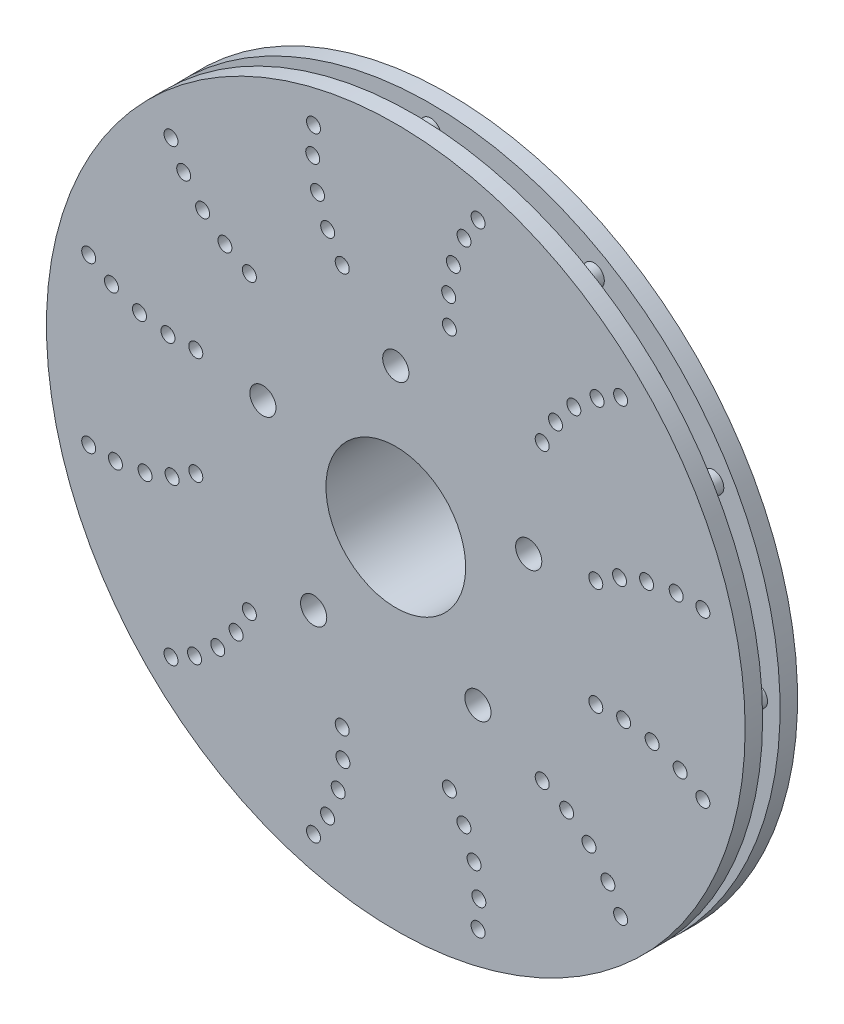
SolidWorks part; units mm, degrees
ref_plane "Front Plane" through (0, 0, 0) normal (0, 0, 1) x (1, 0, 0)
ref_plane "Top Plane" through (0, 0, 0) normal (0, 1, 0) x (1, 0, 0)
ref_plane "Right Plane" through (0, 0, 0) normal (1, 0, 0) x (0, 0, -1)
sketch "Sketch2" plane through (0, 0, 0) normal (0, 0, 1) x (1, 0, 0)
  circle A0 centre (-45.113, 24.0075) radius 25.4
  circle A1 centre (-45.113, 24.0075) radius 60.325
  circle A2 centre (3.2006, 39.7056) radius 4.7625
  circle A3 centre (-45.113, 74.8075) radius 4.7625
  circle A4 centre (-15.2535, -17.0905) radius 4.7625
  circle A5 centre (-74.9725, -17.0905) radius 4.7625
  circle A6 centre (-93.4267, 39.7056) radius 4.7625
extrude "Boss-Extrude1" add sketch "Sketch2" along normal blind 50.8
sketch "Sketch4" plane through (0, 0, 50.8) normal (0, 0, 1) x (1, 0, 0)
  circle A0 centre (-45.113, 24.0075) radius 127
  circle A1 centre (-45.113, 24.0075) radius 60.325
  dimension "D1" = 254
extrude "Boss-Extrude2" add sketch "Sketch4" against normal blind 6.35
sketch "Sketch5" plane through (0, 0, 44.45) normal (0, 0, -1) x (-1, 0, 0)
  line L0 (101.1439, 128.6428) -> (80.2798, 92.5051)
  line L1 (107.7144, 124.8493) -> (86.8503, 88.7117)
  line L2 (48.9065, 142.6398) -> (48.9065, 100.9116)
  line L3 (41.3196, 142.6398) -> (41.3196, 100.9116)
  line L4 (145.9549, 86.6089) -> (109.8172, 65.7448)
  line L5 (149.7483, 80.0384) -> (113.6106, 59.1743)
  line L6 (163.7453, 27.801) -> (122.0171, 27.801)
  line L7 (163.7453, 20.214) -> (122.0171, 20.214)
  line L8 (149.7483, -32.0234) -> (113.6106, -11.1593)
  line L9 (145.9549, -38.5939) -> (109.8172, -17.7298)
  line L10 (107.7144, -76.8343) -> (86.8503, -40.6966)
  line L11 (101.1439, -80.6278) -> (80.2798, -44.4901)
  line L12 (48.9065, -94.6248) -> (48.9065, -52.8965)
  line L13 (41.3196, -94.6248) -> (41.3196, -52.8965)
  line L14 (-10.9179, -80.6278) -> (9.9462, -44.4901)
  line L15 (-17.4884, -76.8343) -> (3.3758, -40.6966)
  line L16 (-55.7288, -38.5939) -> (-19.5911, -17.7298)
  line L17 (-59.5223, -32.0234) -> (-23.3846, -11.1593)
  line L18 (-73.5192, 20.214) -> (-31.791, 20.214)
  line L19 (-73.5192, 27.801) -> (-31.791, 27.801)
  line L20 (-59.5223, 80.0384) -> (-23.3846, 59.1743)
  line L21 (-55.7288, 86.6089) -> (-19.5911, 65.7448)
  line L22 (-17.4884, 124.8493) -> (3.3758, 88.7117)
  line L23 (-10.9179, 128.6428) -> (9.9462, 92.5051)
  arc A1 (48.9065, 142.6398) -> (41.3196, 142.6398) centre (45.113, 142.6398) ccw
  arc A2 (41.3196, 100.9116) -> (48.9065, 100.9116) centre (45.113, 100.9116) ccw
  arc A3 (107.7144, 124.8493) -> (101.1439, 128.6428) centre (104.4292, 126.7461) ccw
  arc A4 (80.2798, 92.5051) -> (86.8503, 88.7117) centre (83.5651, 90.6084) ccw
  arc A5 (149.7483, 80.0384) -> (145.9549, 86.6089) centre (147.8516, 83.3237) ccw
  arc A6 (109.8172, 65.7448) -> (113.6106, 59.1743) centre (111.7139, 62.4595) ccw
  arc A7 (163.7453, 20.214) -> (163.7453, 27.801) centre (163.7453, 24.0075) ccw
  arc A8 (122.0171, 27.801) -> (122.0171, 20.214) centre (122.0171, 24.0075) ccw
  arc A9 (145.9549, -38.5939) -> (149.7483, -32.0234) centre (147.8516, -35.3086) ccw
  arc A10 (113.6106, -11.1593) -> (109.8172, -17.7298) centre (111.7139, -14.4445) ccw
  arc A11 (101.1439, -80.6278) -> (107.7144, -76.8343) centre (104.4292, -78.731) ccw
  arc A12 (86.8503, -40.6966) -> (80.2798, -44.4901) centre (83.5651, -42.5934) ccw
  arc A13 (41.3196, -94.6248) -> (48.9065, -94.6248) centre (45.113, -94.6248) ccw
  arc A14 (48.9065, -52.8965) -> (41.3196, -52.8965) centre (45.113, -52.8965) ccw
  arc A15 (-17.4884, -76.8343) -> (-10.9179, -80.6278) centre (-14.2031, -78.731) ccw
  arc A16 (9.9462, -44.4901) -> (3.3758, -40.6966) centre (6.661, -42.5934) ccw
  arc A17 (-59.5223, -32.0234) -> (-55.7288, -38.5939) centre (-57.6255, -35.3086) ccw
  arc A18 (-19.5911, -17.7298) -> (-23.3846, -11.1593) centre (-21.4878, -14.4445) ccw
  arc A19 (-73.5192, 27.801) -> (-73.5192, 20.214) centre (-73.5192, 24.0075) ccw
  arc A20 (-31.791, 20.214) -> (-31.791, 27.801) centre (-31.791, 24.0075) ccw
  arc A21 (-55.7288, 86.6089) -> (-59.5223, 80.0384) centre (-57.6255, 83.3237) ccw
  arc A22 (-23.3846, 59.1743) -> (-19.5911, 65.7448) centre (-21.4878, 62.4595) ccw
  arc A23 (-10.9179, 128.6428) -> (-17.4884, 124.8493) centre (-14.2031, 126.7461) ccw
  arc A24 (3.3758, 88.7117) -> (9.9462, 92.5051) centre (6.661, 90.6084) ccw
  point P8 (45.113, 121.7757)
  point P77 (45.113, 24.0075)
  dimension "D1" = 12
extrude "Boss-Extrude3" add sketch "Sketch5" along normal blind 6.35
sketch "Sketch6" plane through (0, 0, 38.1) normal (0, 0, -1) x (-1, 0, 0)
  circle A0 centre (45.113, 24.0075) radius 127
  circle A1 centre (45.113, 24.0075) radius 66.675
  dimension "D1" = 133.35
extrude "Boss-Extrude4" add sketch "Sketch6" along normal blind 6.35
sketch "Sketch7" plane through (0, 0, 31.75) normal (0, 0, -1) x (-1, 0, 0)
  circle A1 centre (64.5932, 96.7084) radius 2.54
  circle A2 centre (15.2008, 135.6413) radius 2.54
  circle A3 centre (25.6329, 96.7084) radius 2.54
  circle A4 centre (24.1737, 117.1815) radius 2.54
  circle A5 centre (20.3096, 127.3682) radius 2.54
  circle A6 centre (25.8952, 106.8256) radius 2.54
  circle A7 centre (69.8789, 105.339) radius 2.54
  circle A8 centre (73.566, 115.1682) radius 2.54
  circle A9 centre (75.313, 125.9222) radius 2.54
  circle A10 centre (75.0252, 135.6413) radius 2.54
  circle A11 centre (98.3337, 77.2282) radius 2.54
  circle A12 centre (107.2267, 82.0597) radius 2.54
  circle A13 centre (115.3344, 88.7285) radius 2.54
  circle A14 centre (122.2243, 97.1683) radius 2.54
  circle A15 centre (126.8346, 105.7291) radius 2.54
  circle A16 centre (117.8139, 43.4876) radius 2.54
  circle A17 centre (127.9311, 43.2253) radius 2.54
  circle A18 centre (138.287, 44.9468) radius 2.54
  circle A19 centre (148.4737, 48.8109) radius 2.54
  circle A20 centre (156.7468, 53.9197) radius 2.54
  circle A21 centre (117.8139, 4.5274) radius 2.54
  circle A22 centre (126.4445, -0.7584) radius 2.54
  circle A23 centre (136.2737, -4.4455) radius 2.54
  circle A24 centre (147.0277, -6.1925) radius 2.54
  circle A25 centre (156.7468, -5.9047) radius 2.54
  circle A26 centre (98.3337, -29.2132) radius 2.54
  circle A27 centre (103.1652, -38.1061) radius 2.54
  circle A28 centre (109.834, -46.2138) radius 2.54
  circle A29 centre (118.2738, -53.1038) radius 2.54
  circle A30 centre (126.8346, -57.7141) radius 2.54
  circle A31 centre (64.5932, -48.6933) radius 2.54
  circle A32 centre (64.3309, -58.8106) radius 2.54
  circle A33 centre (66.0523, -69.1664) radius 2.54
  circle A34 centre (69.9164, -79.3532) radius 2.54
  circle A35 centre (75.0252, -87.6263) radius 2.54
  circle A36 centre (25.6329, -48.6933) radius 2.54
  circle A37 centre (20.3471, -57.324) radius 2.54
  circle A38 centre (16.66, -67.1532) radius 2.54
  circle A39 centre (14.913, -77.9072) radius 2.54
  circle A40 centre (15.2008, -87.6263) radius 2.54
  circle A41 centre (-8.1077, -29.2132) radius 2.54
  circle A42 centre (-17.0006, -34.0447) radius 2.54
  circle A43 centre (-25.1083, -40.7134) radius 2.54
  circle A44 centre (-31.9983, -49.1532) radius 2.54
  circle A45 centre (-36.6086, -57.7141) radius 2.54
  circle A46 centre (-27.5878, 4.5274) radius 2.54
  circle A47 centre (-37.705, 4.7897) radius 2.54
  circle A48 centre (-48.0609, 3.0682) radius 2.54
  circle A49 centre (-58.2477, -0.7959) radius 2.54
  circle A50 centre (-66.5208, -5.9047) radius 2.54
  circle A51 centre (-27.5878, 43.4876) radius 2.54
  circle A52 centre (-36.2184, 48.7734) radius 2.54
  circle A53 centre (-46.0476, 52.4605) radius 2.54
  circle A54 centre (-56.8017, 54.2075) radius 2.54
  circle A55 centre (-66.5208, 53.9197) radius 2.54
  circle A56 centre (-8.1077, 77.2282) radius 2.54
  circle A57 centre (-12.9391, 86.1212) radius 2.54
  circle A58 centre (-19.6079, 94.2289) radius 2.54
  circle A59 centre (-28.0477, 101.1188) radius 2.54
  circle A60 centre (-36.6086, 105.7291) radius 2.54
  point P125 (45.113, 24.0075)
  dimension "D1" = 5.08
  dimension "D2" = 5.08
  dimension "D3" = 5.08
  dimension "D4" = 5.08
  dimension "D5" = 5.08
  dimension "D6" = 12
extrude "Cut-Extrude1" cut sketch "Sketch7" against normal blind 84.836
